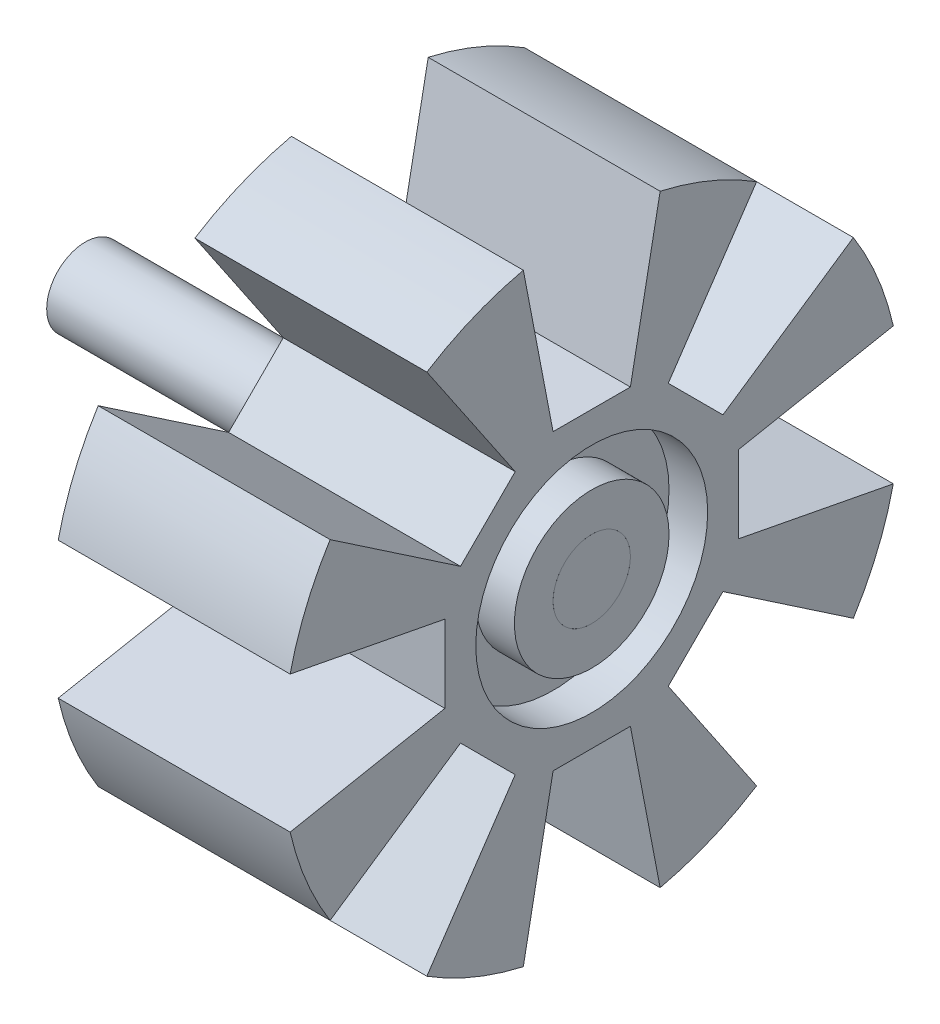
SolidWorks part; units mm, degrees
ref_plane "Front Plane" through (0, 0, 0) normal (0, 0, 1) x (1, 0, 0)
ref_plane "Top Plane" through (0, 0, 0) normal (0, 1, 0) x (1, 0, 0)
ref_plane "Right Plane" through (0, 0, 0) normal (1, 0, 0) x (0, 0, -1)
sketch "Sketch2" plane through (0, 0, 0) normal (0, 0, 1) x (1, 0, 0)
  line L0 (0, 0) -> (-19.0453, 0) construction
  line L1 (0, 5) -> (-30, 5)
  line L2 (-30, 5) -> (-30, 10)
  line L3 (-30, 10) -> (-25, 10)
  line L4 (-25, 10) -> (-25, 15)
  line L5 (-25, 15) -> (-30, 15)
  line L6 (-30, 15) -> (-30, 40)
  line L7 (-30, 40) -> (0, 40)
  line L8 (0, 40) -> (0, 15)
  line L9 (0, 15) -> (-5, 15)
  line L10 (-5, 15) -> (-5, 10)
  line L11 (-5, 10) -> (0, 10)
  line L12 (0, 10) -> (0, 5)
  point P19 (-25, 12.5)
  dimension "D1" = 10
  dimension "D2" = 80
  dimension "D3" = 30
  dimension "D4" = 5
  dimension "D5" = 20
  dimension "D6" = 25
revolve "Revolve1" add sketch "Sketch2" angle 360 about L0
sketch "Sketch8" plane through (-30, 0, 0) normal (-1, 0, 0) x (0, 0, 1)
  line L0 (-10, 45) -> (10, 45)
  line L1 (10, 45) -> (5, 19)
  line L2 (5, 19) -> (-5, 19)
  line L3 (-5, 19) -> (-10, 45)
  circle A0 centre (0, 0) radius 40 construction
  point P2 (0, 45)
  point P5 (0, 19)
  point P9 (0, 40)
  dimension "D1" = 26
  dimension "D2" = 10
  dimension "D3" = 20
  dimension "D4" = 5
extrude "Cut-Extrude6" cut sketch "Sketch8" against normal through all
pattern_circular "CirPattern6" count 8 over 360 about axis through (0, 0, 0) along (1, 0, 0) of "Cut-Extrude6"
sketch "Sketch9" plane through (-30, 0, 0) normal (-1, 0, 0) x (0, 0, 1)
  circle A0 centre (0, 0) radius 5
  point P3 (0, 0)
  point P4 (0, 0)
  point P5 (0, 0)
extrude "Boss-Extrude1" add sketch "Sketch9" along normal blind 35.5 and the other way blind 30 separate body
sketch "Sketch11" plane through (-65.5, 0, 0) normal (-1, 0, 0) x (0, 0, 1)
  circle A0 centre (0, 0) radius 2.95
extrude "Cut-Extrude7" cut sketch "Sketch11" against normal blind 15.5
